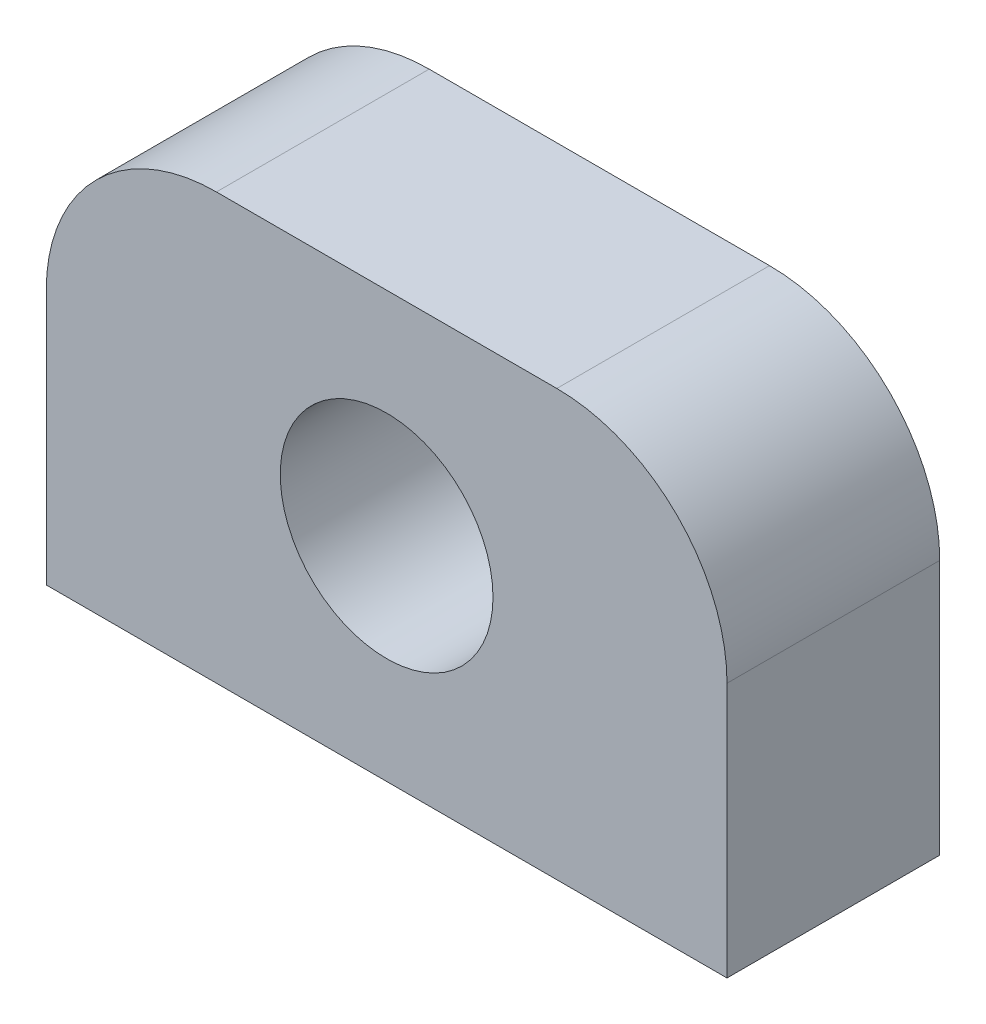
SolidWorks part; units mm, degrees
ref_plane "Front Plane" through (0, 0, 0) normal (0, 0, 1) x (1, 0, 0)
ref_plane "Top Plane" through (0, 0, 0) normal (0, 1, 0) x (1, 0, 0)
ref_plane "Right Plane" through (0, 0, 0) normal (1, 0, 0) x (0, 0, -1)
sketch "Sketch1" plane through (0, 0, 0) normal (0, 0, 1) x (1, 0, 0)
  line L0 (0, 0) -> (20.32, 12.7) construction
  line L1 (0, 0) -> (20.32, 0)
  line L2 (0, 0) -> (0, 7.62)
  line L3 (5.08, 12.7) -> (15.24, 12.7)
  line L4 (20.32, 0) -> (20.32, 7.62)
  line L5 (0, 12.7) -> (20.32, 0) construction
  circle A0 centre (10.16, 6.35) radius 3.175
  arc A1 (5.08, 12.7) -> (0, 7.62) centre (5.08, 7.62) ccw
  arc A2 (20.32, 7.62) -> (15.24, 12.7) centre (15.24, 7.62) ccw
  dimension "D3" = 6.35
  dimension "D4" = 5.08
  dimension "D5" = 5.08
  dimension "D1" = 12.7
  dimension "D2" = 20.32
  dimension "D6" = 90
extrude "Boss-Extrude1" add sketch "Sketch1" along normal blind 6.35
